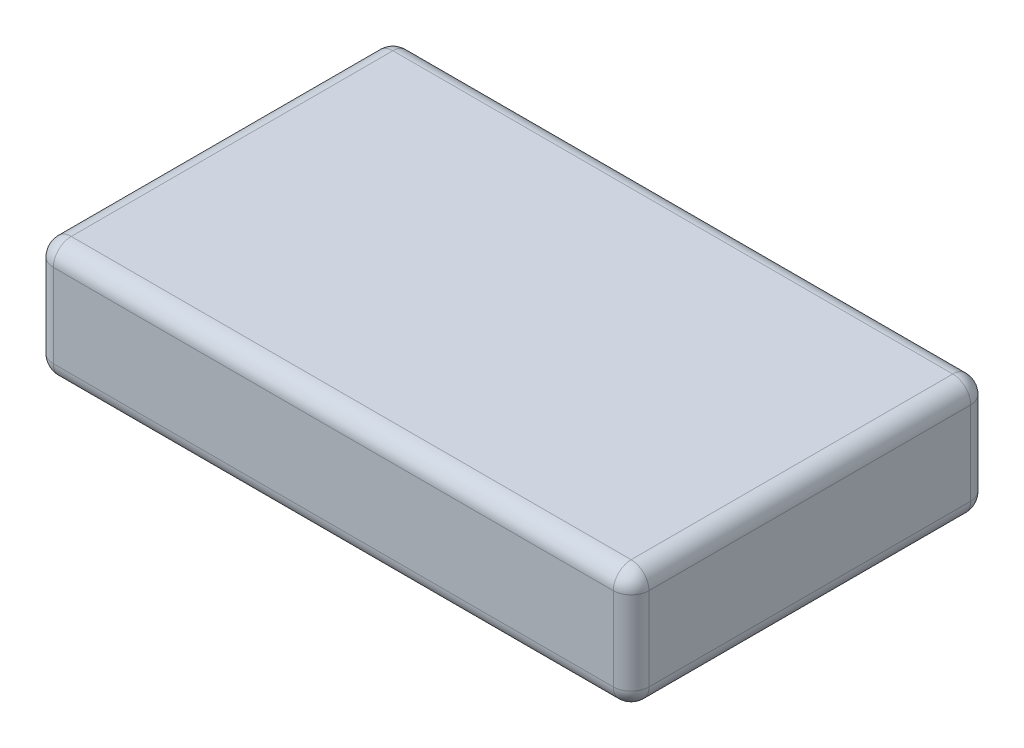
SolidWorks part; units mm, degrees
ref_plane "前视基准面" through (0, 0, 0) normal (0, 0, 1) x (1, 0, 0)
ref_plane "上视基准面" through (0, 0, 0) normal (0, 1, 0) x (1, 0, 0)
ref_plane "右视基准面" through (0, 0, 0) normal (1, 0, 0) x (0, 0, -1)
sketch "草图1" plane through (0, 0, 0) normal (0, 1, 0) x (1, 0, 0)
  line L1 (-50, 30) -> (50, 30)
  line L2 (-50, 30) -> (-50, -30)
  line L3 (-50, -30) -> (50, -30)
  line L4 (50, 30) -> (50, -30)
  line L5 (-50, 30) -> (50, -30) construction
  line L6 (-50, -30) -> (50, 30) construction
  point P0 (0, 0)
  dimension "D1" = 100
  dimension "D2" = 60
extrude "凸台-拉伸1" add sketch "草图1" along normal blind 20
fillet "圆角1" radius 3 12 edges at (0, 20, -30) (0, 0, 30) (50, 10, 30) (-50, 20, 0) (-50, 0, 0) (0, 0, -30) (50, 0, 0) (50, 20, 0) (0, 20, 30) (50, 10, -30) (-50, 10, -30) (-50, 10, 30)
